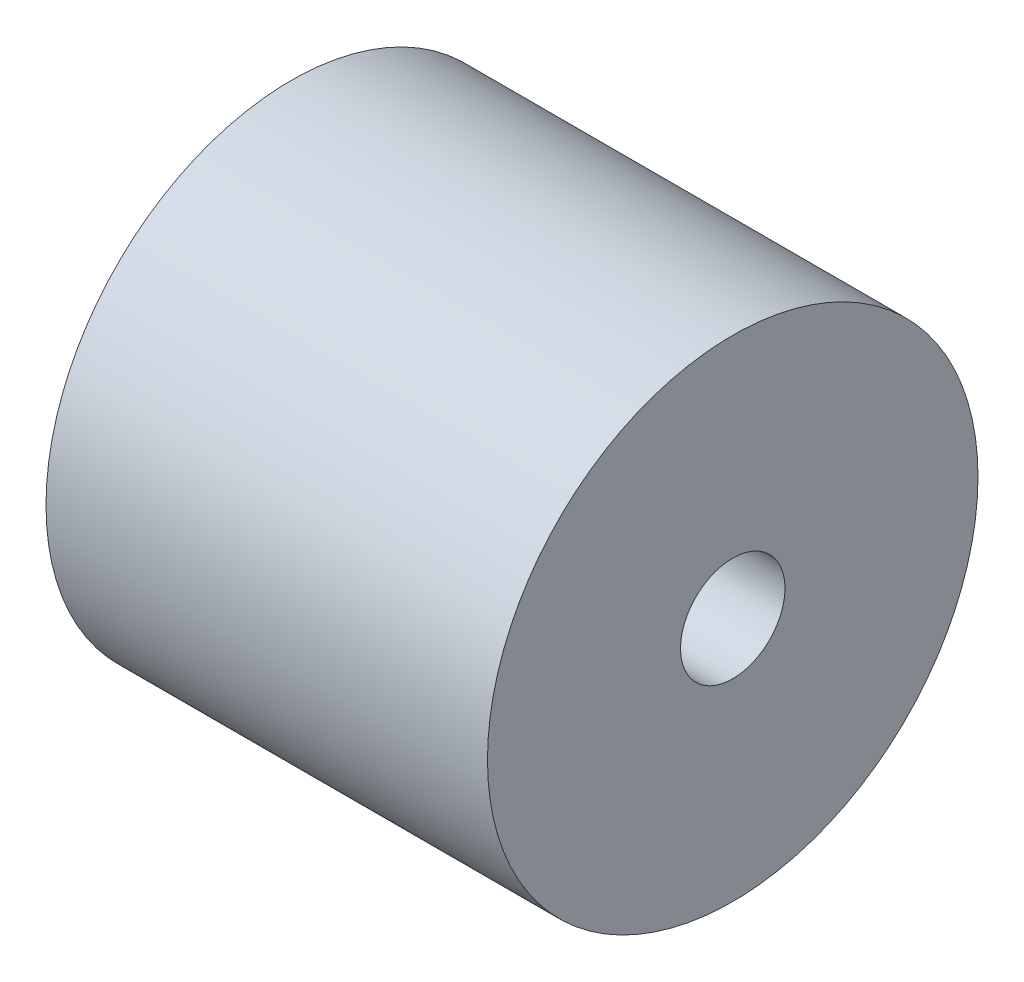
SolidWorks part; units mm, degrees
ref_plane "Front Plane" through (0, 0, 0) normal (0, 0, 1) x (1, 0, 0)
ref_plane "Top Plane" through (0, 0, 0) normal (0, 1, 0) x (1, 0, 0)
ref_plane "Right Plane" through (0, 0, 0) normal (1, 0, 0) x (0, 0, -1)
sketch "Sketch1" plane through (0, 0, 0) normal (1, 0, 0) x (0, 0, -1)
  circle A0 centre (0, 0) radius 6.35
  dimension "D1" = 12.7
extrude "Boss-Extrude1" add sketch "Sketch1" along normal blind 11.43
sketch "Sketch2" plane through (0, 0, 0) normal (-1, 0, 0) x (0, 0, 1)
  circle A0 centre (0, 0) radius 1.7526
  dimension "D1" = 3.5052
sketch "Sketch3" plane through (11.43, 0, 0) normal (1, 0, 0) x (0, 0, -1)
  circle A0 centre (0, 0) radius 1.5875
  dimension "D1" = 3.175
hole_wizard "#6-32 Tapped Hole1" positions "Sketch4" profile "Sketch5" tap size "#6-32" standard "ANSI Inch" end condition through all
sketch "Sketch4" plane through (0, 0, 0) normal (-1, 0, 0) x (0, 0, 1)
  point P0 (0, 0)
cosmetic thread "Hole Thread1" parameters "D2"=3.5052
sketch "Sketch5" plane through (0, 0, 0) normal (0, 1, 0) x (0, 0, 1)
  line L0 (0, 0) -> (0, 11.43)
  line L1 (0, 11.43) -> (1.3525, 11.43)
  line L2 (1.3525, 11.43) -> (1.3525, 0)
  line L5 (1.3525, 0) -> (0, 0)
  line L11 (0, -6.35) -> (0, 107.95) construction
  dimension "Thru Tap Drill Dia." = 2.7051
  dimension "Thru Tap Drill Depth" = 11.43
